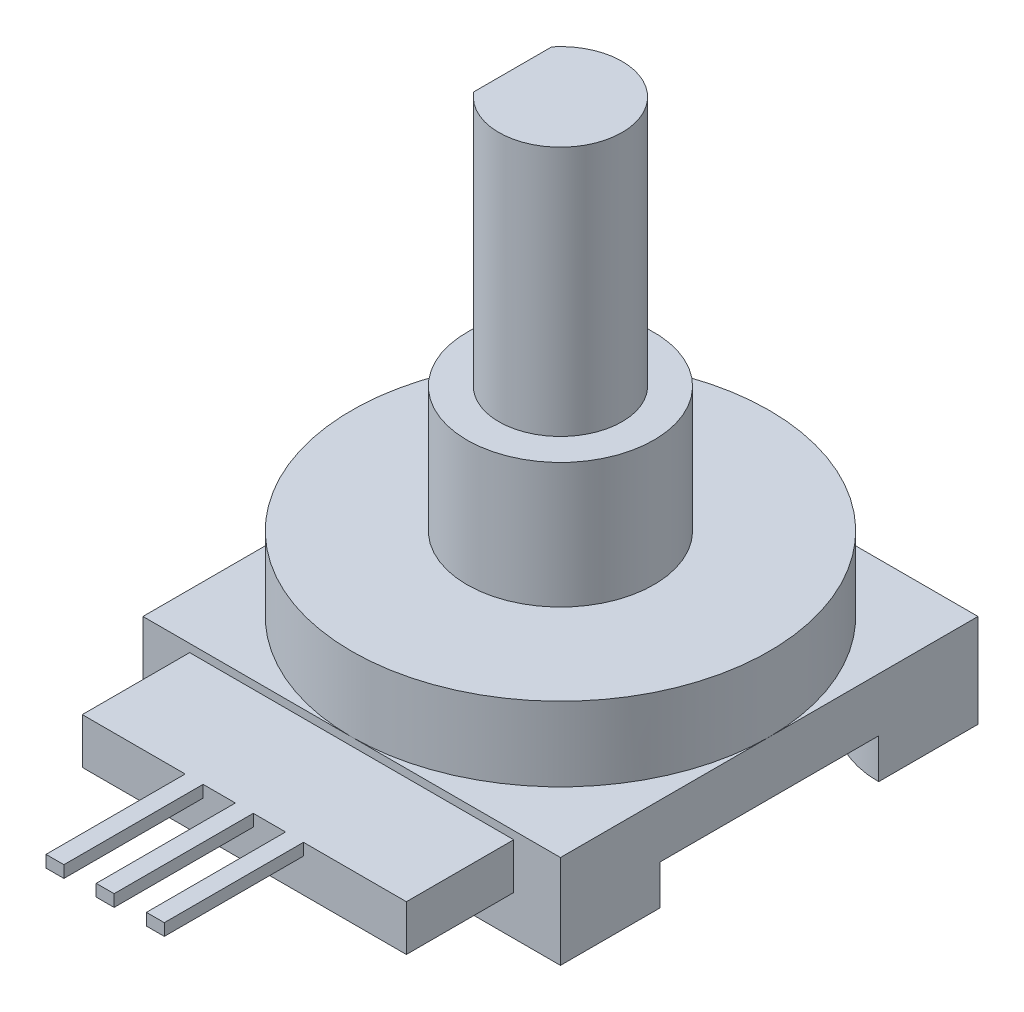
SolidWorks part; units mm, degrees
ref_plane "Front Plane" through (0, 0, 0) normal (0, 0, 1) x (1, 0, 0)
ref_plane "Top Plane" through (0, 0, 0) normal (0, 1, 0) x (1, 0, 0)
ref_plane "Right Plane" through (0, 0, 0) normal (1, 0, 0) x (0, 0, -1)
sketch "Sketch1" plane through (0, 0, 0) normal (0, 1, 0) x (1, 0, 0)
  line L1 (0, 0) -> (21, 0)
  line L2 (0, 0) -> (0, 21)
  line L3 (0, 21) -> (21, 21)
  line L4 (21, 0) -> (21, 21)
  dimension "D1" = 21
  dimension "D2" = 21
extrude "Boss-Extrude1" add sketch "Sketch1" along normal blind 4.7
sketch "Sketch2" plane through (0, 4.7, 0) normal (0, 1, 0) x (1, 0, 0)
  line L0 (10.5, 21) -> (10.5, 0) construction
  line L1 (21, 21) -> (0, 21) construction
  line L2 (0, 0) -> (21, 0) construction
  circle A0 centre (10.5, 10.5) radius 10.5
extrude "Boss-Extrude2" add sketch "Sketch2" along normal blind 3.73
sketch "Sketch3" plane through (0, 8.43, 0) normal (0, 1, 0) x (1, 0, 0)
  circle A0 centre (10.5, 10.5) radius 4.7
  dimension "D1" = 9.4
extrude "Boss-Extrude3" add sketch "Sketch3" along normal blind 6.3
sketch "Sketch4" plane through (0, 14.73, 0) normal (0, 1, 0) x (1, 0, 0)
  circle A0 centre (10.5, 10.5) radius 3.1
  dimension "D1" = 6.2
extrude "Boss-Extrude4" add sketch "Sketch4" along normal blind 12.6
sketch "Sketch5" plane through (0, 0, 0) normal (0, -1, 0) x (1, 0, 0)
  line L0 (10.5, 0) -> (10.5, -21) construction
  line L1 (0, 0) -> (21, 0) construction
  line L2 (21, -21) -> (0, -21) construction
  line L3 (21, -10.5) -> (0, -10.5) construction
  line L5 (5, 0) -> (16, 0)
  line L6 (0, -5) -> (0, -16)
  line L7 (5, -21) -> (16, -21)
  line L8 (21, -5) -> (21, -16)
  arc A0 (0, -5) -> (5, 0) centre (0, 0) ccw
  arc A1 (21, -5) -> (16, 0) centre (21, 0) cw
  arc A2 (21, -16) -> (16, -21) centre (21, -21) ccw
  arc A3 (0, -16) -> (5, -21) centre (0, -21) cw
  dimension "D1" = 10
extrude "Cut-Extrude1" cut sketch "Sketch5" against normal blind 2
sketch "Sketch6" plane through (0, 0, 0) normal (0, 0, 1) x (1, 0, 0)
  line L0 (0, 4.7) -> (21, 4.7) construction
  line L1 (2.35, 4.3) -> (18.65, 4.3)
  line L2 (2.35, 4.3) -> (2.35, 2)
  line L3 (2.35, 2) -> (18.65, 2)
  line L4 (18.65, 4.3) -> (18.65, 2)
  line L5 (0, 0) -> (5, 0) construction
  point P8 (10.5, 4.3)
  dimension "D1" = 16.3
  dimension "D2" = 2.3
  dimension "D3" = 2
extrude "Boss-Extrude5" add sketch "Sketch6" along normal blind 5.4
sketch "Sketch7" plane through (0, 0, 5.4) normal (0, 0, 1) x (1, 0, 0)
  line L0 (18.65, 4.3) -> (2.35, 4.3) construction
  line L1 (7.525, 4.3) -> (13.475, 4.3)
  line L2 (7.525, 4.3) -> (7.525, 3.7)
  line L3 (7.525, 3.7) -> (13.475, 3.7)
  line L4 (13.475, 4.3) -> (13.475, 3.7)
  line L5 (2.35, 2) -> (18.65, 2) construction
  point P6 (10.5, 2)
  point P9 (10.5, 3.7)
  dimension "D1" = 5.95
  dimension "D2" = 0.6
extrude "Boss-Extrude6" add sketch "Sketch7" along normal blind 7
sketch "Sketch8" plane through (0, 4.3, 0) normal (0, 1, 0) x (1, 0, 0)
  line L0 (7.525, -5.4) -> (13.475, -5.4) construction
  line L1 (13.475, -12.4) -> (7.525, -12.4) construction
  line L2 (13.475, -12.4) -> (13.475, -5.4) construction
  line L3 (8.425, -12.4) -> (10.05, -12.4)
  line L4 (8.425, -12.4) -> (8.425, -5.4)
  line L5 (8.425, -5.4) -> (10.05, -5.4)
  line L6 (10.05, -12.4) -> (10.05, -5.4)
  line L7 (10.95, -12.4) -> (12.575, -12.4)
  line L8 (10.95, -12.4) -> (10.95, -5.4)
  line L9 (10.95, -5.4) -> (12.575, -5.4)
  line L10 (12.575, -12.4) -> (12.575, -5.4)
  dimension "D1" = 0.9
  dimension "D2" = 0.9
  dimension "D3" = 0.9
  dimension "D4" = 1.625
extrude "Cut-Extrude2" cut sketch "Sketch8" against normal through all and the other way through all
sketch "Sketch9" plane through (0, 27.33, 0) normal (0, 1, 0) x (1, 0, 0)
  line L0 (8.1, 12.4621) -> (8.1, 8.5379)
  line L1 (13.6, 13.1271) -> (13.6, 7.7501) construction
  circle A0 centre (10.5, 10.5) radius 3.1 construction
  circle A1 centre (10.5, 10.5) radius 3.1 construction
  arc A2 (8.1, 12.4621) -> (8.1, 8.5379) centre (10.5, 10.5) ccw
  dimension "D1" = 5.5
extrude "Cut-Extrude3" cut sketch "Sketch9" against normal blind 9.64
